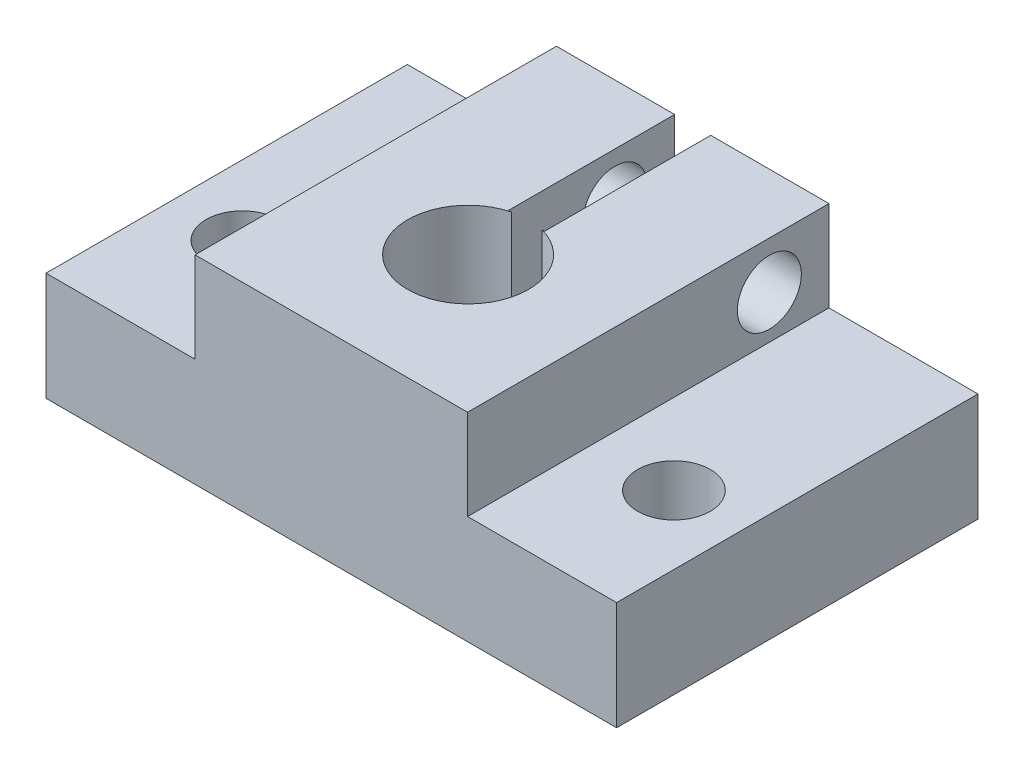
SolidWorks part; units mm, degrees
ref_plane "Front Plane" through (0, 0, 0) normal (0, 0, 1) x (1, 0, 0)
ref_plane "Top Plane" through (0, 0, 0) normal (0, 1, 0) x (1, 0, 0)
ref_plane "Right Plane" through (0, 0, 0) normal (1, 0, 0) x (0, 0, -1)
sketch "Sketch1" plane through (0, 0, 0) normal (0, 0, 1) x (1, 0, 0)
  line L0 (-20.0526, 0) -> (-20.0526, 7.62)
  line L1 (-20.0526, 7.62) -> (-9.5771, 7.62)
  line L2 (-9.5771, 7.62) -> (-9.5771, 13.97)
  line L3 (-9.5771, 13.97) -> (9.5771, 13.97)
  line L4 (0, 13.97) -> (0, 0) construction
  line L5 (-20.0526, 0) -> (20.0526, 0)
  line L6 (20.0526, 0) -> (20.0526, 7.62)
  line L7 (20.0526, 7.62) -> (9.5771, 7.62)
  line L8 (9.5771, 7.62) -> (9.5771, 13.97)
  dimension "D1" = 7.62
  dimension "D2" = 6.35
extrude "Boss-Extrude1" add sketch "Sketch1" along normal blind 25.4
ref_plane "Plane1" through (20.0526, 7.62, 25.4) normal (0, 1, 0) x (1, 0, 0)
ref_plane "Plane2" through (20.0526, 7.62, 25.4) normal (0, 1, 0) x (1, 0, 0)
sketch "Sketch6" plane through (0, 13.97, 0) normal (0, 1, 0) x (1, 0, 0)
  circle A0 centre (0, -15.7882) radius 4.25
  dimension "D1" = 8.5
extrude "Cut-Extrude1" cut sketch "Sketch6" against normal through all
ref_plane "Plane3" through (-9.5771, 13.97, 0) normal (-1, 0, 0) x (0, 0, 1)
sketch "Sketch11" plane through (0, 7.62, 0) normal (0, 1, 0) x (1, 0, 0)
  point P0 (0, 0)
  point P3 (0.0986, -16.5565)
sketch "Sketch12" plane through (0, 7.62, 0) normal (0, 1, 0) x (1, 0, 0)
  line L0 (-9.5771, -25.4) -> (-20.0526, -25.4) construction
  circle A0 centre (-15.1413, -16.51) radius 2.5527
  circle A1 centre (15.24, -16.5565) radius 2.5527
  circle A2 centre (0, -15.7882) radius 4.25 construction
  point P4 (0.0986, -16.5565)
  dimension "D1" = 5.1054
  dimension "D2" = 15.24
  dimension "D3" = 15.24
  dimension "D4" = 8.89
extrude "Cut-Extrude2" cut sketch "Sketch12" against normal through all
sketch "Sketch13" plane through (0, 0, 25.4) normal (0, 0, 1) x (1, 0, 0)
sketch "Sketch14" plane through (0, 13.97, 0) normal (0, 1, 0) x (1, 0, 0)
  line L1 (9.5771, 0) -> (-9.5771, 0) construction
  line L2 (0, 0) -> (0, -11.5382) construction
  line L3 (-1.27, 0) -> (1.27, 0)
  line L6 (-1.27, -11.6999) -> (-1.27, 0)
  line L7 (-1.27, -11.6999) -> (0, -11.5382)
  line L8 (1.27, -11.6999) -> (0, -11.5382)
  line L9 (1.27, -11.6999) -> (1.27, 0)
  circle A0 centre (0, -15.7882) radius 4.25 construction
  point P9 (-0.635, -11.619)
  point P10 (0, -7.9031)
  point P14 (0.635, -11.619)
  dimension "D1" = 1.27
extrude "Cut-Extrude3" cut sketch "Sketch14" against normal through all
sketch "Sketch16" plane through (9.5771, 0, 0) normal (1, 0, 0) x (0, 0, -1)
  line L0 (-4.189, 13.97) -> (-4.189, 12.8584) construction
  line L1 (-25.4, 13.97) -> (0, 13.97) construction
  circle A5 centre (-4.189, 10.668) radius 2.2499
  dimension "D1" = 4.4999
  dimension "D2" = 3.302
extrude "Cut-Extrude8" cut sketch "Sketch16" against normal through all
